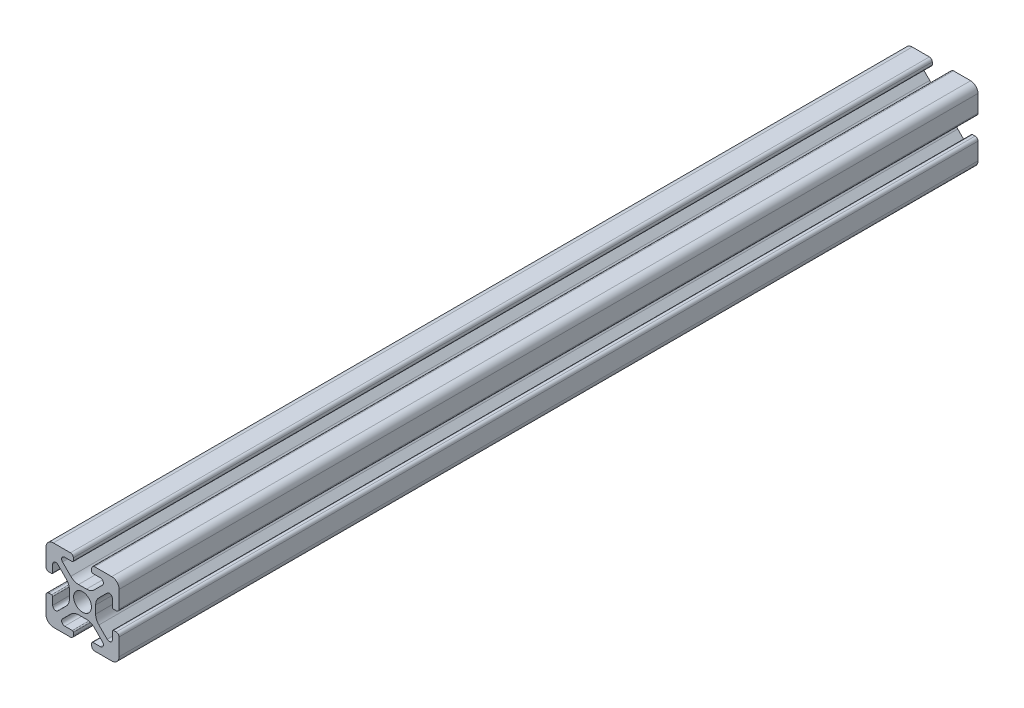
SolidWorks part; units mm, degrees
material "1060 Alloy"
ref_plane "Front Plane" through (0, 0, 0) normal (0, 0, 1) x (1, 0, 0)
ref_plane "Top Plane" through (0, 0, 0) normal (0, 1, 0) x (1, 0, 0)
ref_plane "Right Plane" through (0, 0, 0) normal (1, 0, 0) x (0, 0, -1)
sketch "Sketch1" plane through (0, 0, 0) normal (0, 0, 1) x (1, 0, 0)
  line L0 (0, 9.98) -> (0, -9.7791) construction
  line L1 (-9.98, 0) -> (10.2107, 0) construction
  line L2 (-9.98, 7.9734) -> (-9.98, 3.2974)
  line L3 (-7.9734, 9.98) -> (-3.2974, 9.98)
  line L4 (-2.51, 9.1926) -> (-2.51, 8.4514)
  line L5 (-2.8148, 8.1466) -> (-4.87, 8.1466)
  line L6 (-5.4627, 6.7157) -> (-3.2079, 4.4609)
  line L7 (-6.7157, 5.4627) -> (-4.4609, 3.2079)
  line L8 (-8.1466, 4.87) -> (-8.1466, 2.8148)
  line L9 (-8.4514, 2.51) -> (-9.1926, 2.51)
  line L10 (0, 0) -> (-9.98, 9.98) construction
  line L11 (-1.0885, 3.583) -> (1.0885, 3.583)
  line L12 (-3.583, 1.0885) -> (-3.583, -1.0885)
  line L13 (8.4514, 2.51) -> (9.1926, 2.51)
  line L14 (8.1466, 4.87) -> (8.1466, 2.8148)
  line L15 (9.98, 7.9734) -> (9.98, 3.2974)
  line L16 (7.9734, 9.98) -> (3.2974, 9.98)
  line L17 (2.51, 9.1926) -> (2.51, 8.4514)
  line L18 (2.8148, 8.1466) -> (4.87, 8.1466)
  line L19 (3.583, 1.0885) -> (3.583, -1.0885)
  line L20 (5.4627, 6.7157) -> (3.2079, 4.4609)
  line L21 (6.7157, 5.4627) -> (4.4609, 3.2079)
  line L22 (-8.4514, -2.51) -> (-9.1926, -2.51)
  line L23 (-8.1466, -4.87) -> (-8.1466, -2.8148)
  line L24 (-6.7157, -5.4627) -> (-4.4609, -3.2079)
  line L25 (-5.4627, -6.7157) -> (-3.2079, -4.4609)
  line L26 (-2.8148, -8.1466) -> (-4.87, -8.1466)
  line L27 (-2.51, -9.1926) -> (-2.51, -8.4514)
  line L28 (-7.9734, -9.98) -> (-3.2974, -9.98)
  line L29 (-9.98, -7.9734) -> (-9.98, -3.2974)
  line L30 (9.98, -7.9734) -> (9.98, -3.2974)
  line L31 (7.9734, -9.98) -> (3.2974, -9.98)
  line L32 (2.51, -9.1926) -> (2.51, -8.4514)
  line L33 (2.8148, -8.1466) -> (4.87, -8.1466)
  line L34 (5.4627, -6.7157) -> (3.2079, -4.4609)
  line L35 (6.7157, -5.4627) -> (4.4609, -3.2079)
  line L36 (8.1466, -4.87) -> (8.1466, -2.8148)
  line L37 (8.4514, -2.51) -> (9.1926, -2.51)
  line L38 (-1.0885, -3.583) -> (1.0885, -3.583)
  circle A0 centre (0, 0) radius 2.44
  arc A1 (-9.98, 7.9734) -> (-7.9734, 9.98) centre (-7.9734, 7.9734) cw
  arc A2 (-6.7157, 5.4627) -> (-8.1466, 4.87) centre (-7.3084, 4.87) ccw
  arc A3 (-4.87, 8.1466) -> (-5.4627, 6.7157) centre (-4.87, 7.3084) ccw
  arc A4 (-3.2974, 9.98) -> (-2.51, 9.1926) centre (-3.2974, 9.1926) cw
  arc A5 (-9.98, 3.2974) -> (-9.1926, 2.51) centre (-9.1926, 3.2974) ccw
  arc A6 (-8.1466, 2.8148) -> (-8.4514, 2.51) centre (-8.4514, 2.8148) cw
  arc A7 (-2.51, 8.4514) -> (-2.8148, 8.1466) centre (-2.8148, 8.4514) cw
  arc A8 (-1.0885, 3.583) -> (-3.2079, 4.4609) centre (-1.0885, 6.5802) cw
  arc A9 (-3.583, 1.0885) -> (-4.4609, 3.2079) centre (-6.5802, 1.0885) ccw
  arc A10 (8.1466, 2.8148) -> (8.4514, 2.51) centre (8.4514, 2.8148) ccw
  arc A11 (9.98, 3.2974) -> (9.1926, 2.51) centre (9.1926, 3.2974) cw
  arc A12 (9.98, 7.9734) -> (7.9734, 9.98) centre (7.9734, 7.9734) ccw
  arc A13 (3.2974, 9.98) -> (2.51, 9.1926) centre (3.2974, 9.1926) ccw
  arc A14 (2.51, 8.4514) -> (2.8148, 8.1466) centre (2.8148, 8.4514) ccw
  arc A15 (1.0885, 3.583) -> (3.2079, 4.4609) centre (1.0885, 6.5802) ccw
  arc A16 (3.583, 1.0885) -> (4.4609, 3.2079) centre (6.5802, 1.0885) cw
  arc A17 (6.7157, 5.4627) -> (8.1466, 4.87) centre (7.3084, 4.87) cw
  arc A18 (4.87, 8.1466) -> (5.4627, 6.7157) centre (4.87, 7.3084) cw
  arc A19 (-3.583, -1.0885) -> (-4.4609, -3.2079) centre (-6.5802, -1.0885) cw
  arc A20 (-1.0885, -3.583) -> (-3.2079, -4.4609) centre (-1.0885, -6.5802) ccw
  arc A21 (-2.51, -8.4514) -> (-2.8148, -8.1466) centre (-2.8148, -8.4514) ccw
  arc A22 (-8.1466, -2.8148) -> (-8.4514, -2.51) centre (-8.4514, -2.8148) ccw
  arc A23 (-9.98, -3.2974) -> (-9.1926, -2.51) centre (-9.1926, -3.2974) cw
  arc A24 (-3.2974, -9.98) -> (-2.51, -9.1926) centre (-3.2974, -9.1926) ccw
  arc A25 (-4.87, -8.1466) -> (-5.4627, -6.7157) centre (-4.87, -7.3084) cw
  arc A26 (-6.7157, -5.4627) -> (-8.1466, -4.87) centre (-7.3084, -4.87) cw
  arc A27 (-9.98, -7.9734) -> (-7.9734, -9.98) centre (-7.9734, -7.9734) ccw
  arc A28 (9.98, -7.9734) -> (7.9734, -9.98) centre (7.9734, -7.9734) cw
  arc A29 (6.7157, -5.4627) -> (8.1466, -4.87) centre (7.3084, -4.87) ccw
  arc A30 (4.87, -8.1466) -> (5.4627, -6.7157) centre (4.87, -7.3084) ccw
  arc A31 (3.2974, -9.98) -> (2.51, -9.1926) centre (3.2974, -9.1926) cw
  arc A32 (9.98, -3.2974) -> (9.1926, -2.51) centre (9.1926, -3.2974) ccw
  arc A33 (8.1466, -2.8148) -> (8.4514, -2.51) centre (8.4514, -2.8148) cw
  arc A34 (2.51, -8.4514) -> (2.8148, -8.1466) centre (2.8148, -8.4514) cw
  arc A35 (1.0885, -3.583) -> (3.2079, -4.4609) centre (1.0885, -6.5802) cw
  arc A36 (3.583, -1.0885) -> (4.4609, -3.2079) centre (6.5802, -1.0885) ccw
  point P62 (0, 3.583)
  point P116 (0, 0)
  dimension "D1" = 0.8382
  dimension "D2" = 0.3048
  dimension "D3" = 0.7874
  dimension "D4" = 2.0066
  dimension "D9" = 2.9972
  dimension "D12" = 4.88
  dimension "D5" = 19.96
  dimension "D6" = 19.96
  dimension "D7" = 5.02
  dimension "D8" = 1.772
  dimension "D10" = 3.1888
  dimension "D11" = 2.177
extrude "Boss-Extrude1" add sketch "Sketch1" along normal mid plane 234.6
